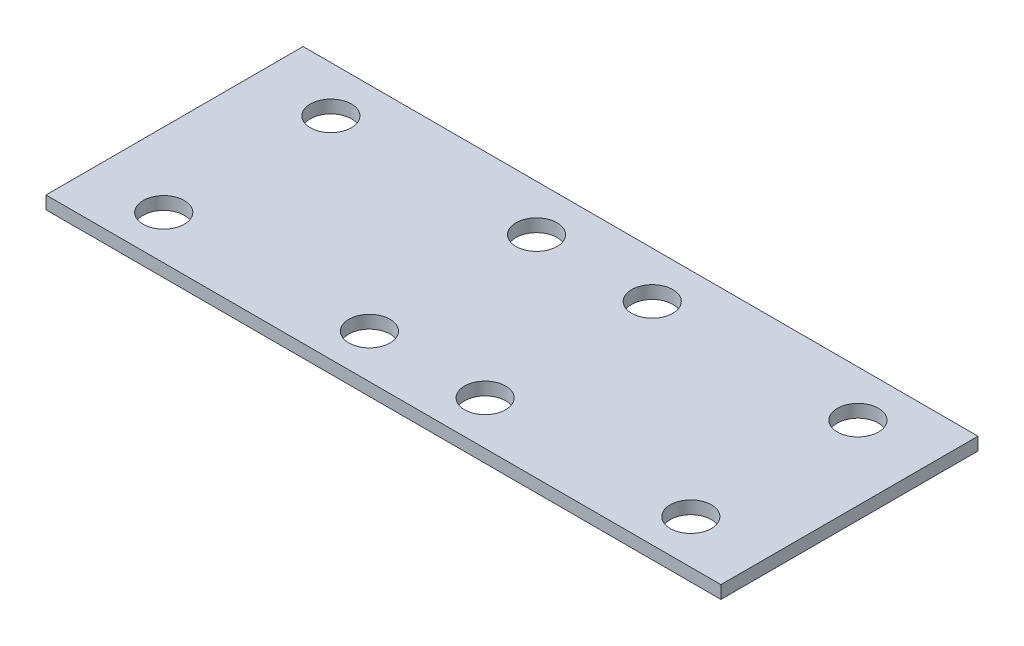
SolidWorks part; units mm, degrees
ref_plane "Front Plane" through (0, 0, 0) normal (0, 0, 1) x (1, 0, 0)
ref_plane "Top Plane" through (0, 0, 0) normal (0, 1, 0) x (1, 0, 0)
ref_plane "Right Plane" through (0, 0, 0) normal (1, 0, 0) x (0, 0, -1)
sketch "Sketch1" plane through (0, 0, 0) normal (0, 1, 0) x (1, 0, 0)
  line L1 (-26.25, -10) -> (26.25, -10)
  line L2 (-26.25, -10) -> (-26.25, 10)
  line L3 (-26.25, 10) -> (26.25, 10)
  line L4 (26.25, -10) -> (26.25, 10)
  line L5 (-26.25, -10) -> (26.25, 10) construction
  line L6 (-26.25, 10) -> (26.25, -10) construction
  point P0 (0, 0)
  dimension "D1" = 20
  dimension "D2" = 52.5
extrude "Boss-Extrude1" add sketch "Sketch1" along normal blind 1
sketch "Sketch2" plane through (0, 1, 0) normal (0, 1, 0) x (1, 0, 0)
  line L0 (0, -0.55) -> (0, 0.55) construction
  circle A2 centre (-20.5, 6.4091) radius 1.6
  circle A3 centre (-4.5, 6.4091) radius 1.6
  circle A4 centre (4.5, 6.4091) radius 1.6
  circle A5 centre (20.5, 6.4091) radius 1.6
  circle A6 centre (-20.5, -6.5909) radius 1.6
  circle A7 centre (-4.5, -6.5909) radius 1.6
  circle A8 centre (4.5, -6.5909) radius 1.6
  circle A9 centre (20.5, -6.5909) radius 1.6
  point P8 (4.1201, 6.4091)
  dimension "D1" = 3.2
  dimension "D2" = 16
  dimension "D4" = 16
  dimension "D5" = 9
  dimension "D6" = 4.5
  dimension "D8" = 16
  dimension "D10" = 16
  dimension "D11" = 9
  dimension "D12" = 13
extrude "Cut-Extrude1" cut sketch "Sketch2" against normal blind 2
